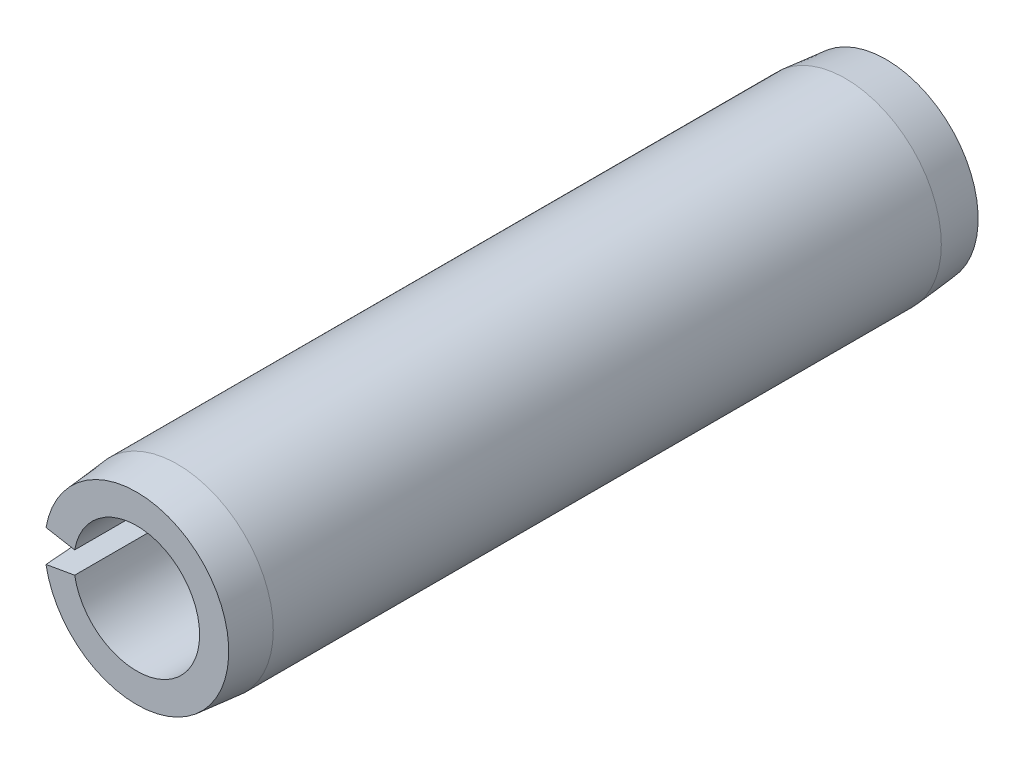
SolidWorks part; units mm, degrees
ref_plane "Front Plane" through (0, 0, 0) normal (0, 0, 1) x (1, 0, 0)
ref_plane "Top Plane" through (0, 0, 0) normal (0, 1, 0) x (1, 0, 0)
ref_plane "Right Plane" through (0, 0, 0) normal (1, 0, 0) x (0, 0, -1)
sketch "Sketch1" plane through (0, 0, 0) normal (0, 0, 1) x (1, 0, 0)
  line L0 (3.7338, 0) -> (5.6896, 0) construction
  line L1 (-5.6032, 0.988) -> (-3.6771, 0.6484)
  line L2 (-3.6771, -0.6484) -> (-5.6032, -0.988)
  arc A0 (-5.6032, -0.988) -> (-5.6032, 0.988) centre (0, 0) ccw
  arc A1 (-3.6771, -0.6484) -> (-3.6771, 0.6484) centre (0, 0) ccw
  dimension "OD" = 11.3792
  dimension "Wall thickness" = 1.9558
  dimension "D3" = 20
extrude "Extrude1" add sketch "Sketch1" along normal mid plane 44.45
sketch "Sketch2" plane through (0, 0, 0) normal (1, 0, 0) x (0, 0, -1)
  line L0 (0, -5.6896) -> (0, 5.6896) construction
  line L1 (22.225, 0) -> (-22.225, 0) construction
  line L2 (22.225, -3.7338) -> (22.225, 3.7338) construction
  line L3 (22.225, 5.6896) -> (-22.225, 5.6896) construction
  line L4 (22.225, 5.6896) -> (22.225, 5.461)
  line L5 (22.225, 5.461) -> (19.812, 5.6896)
  line L6 (19.812, 5.6896) -> (22.225, 5.6896)
  line L7 (22.225, -5.6896) -> (22.225, 5.6896) construction
  line L8 (-19.812, 5.6896) -> (-22.225, 5.6896)
  line L9 (-22.225, 5.461) -> (-19.812, 5.6896)
  line L10 (-22.225, 5.6896) -> (-22.225, 5.461)
  line L11 (19.812, -5.6896) -> (22.225, -5.6896) construction
  line L12 (22.225, -5.461) -> (19.812, -5.6896) construction
  line L13 (22.225, -5.6896) -> (22.225, -5.461) construction
  dimension "B" = 10.922
  dimension "Chamfer max" = 2.413
revolve "Cut-Revolve1" cut sketch "Sketch2" angle 360 about L1
sketch "Sketch3" plane through (0, 0, 0) normal (0, 0, 1) x (1, 0, 0)
  line L0 (3.7338, 0) -> (5.6896, 0) construction
  line L1 (3.7338, 0) -> (5.6896, 0)
  circle A0 centre (0, 0) radius 5.6896
  circle A1 centre (0, 0) radius 3.7338
  arc A2 (-5.6032, -0.988) -> (-5.6032, 0.988) centre (0, 0) ccw construction
  arc A3 (-3.6771, -0.6484) -> (-3.6771, 0.6484) centre (0, 0) ccw construction
